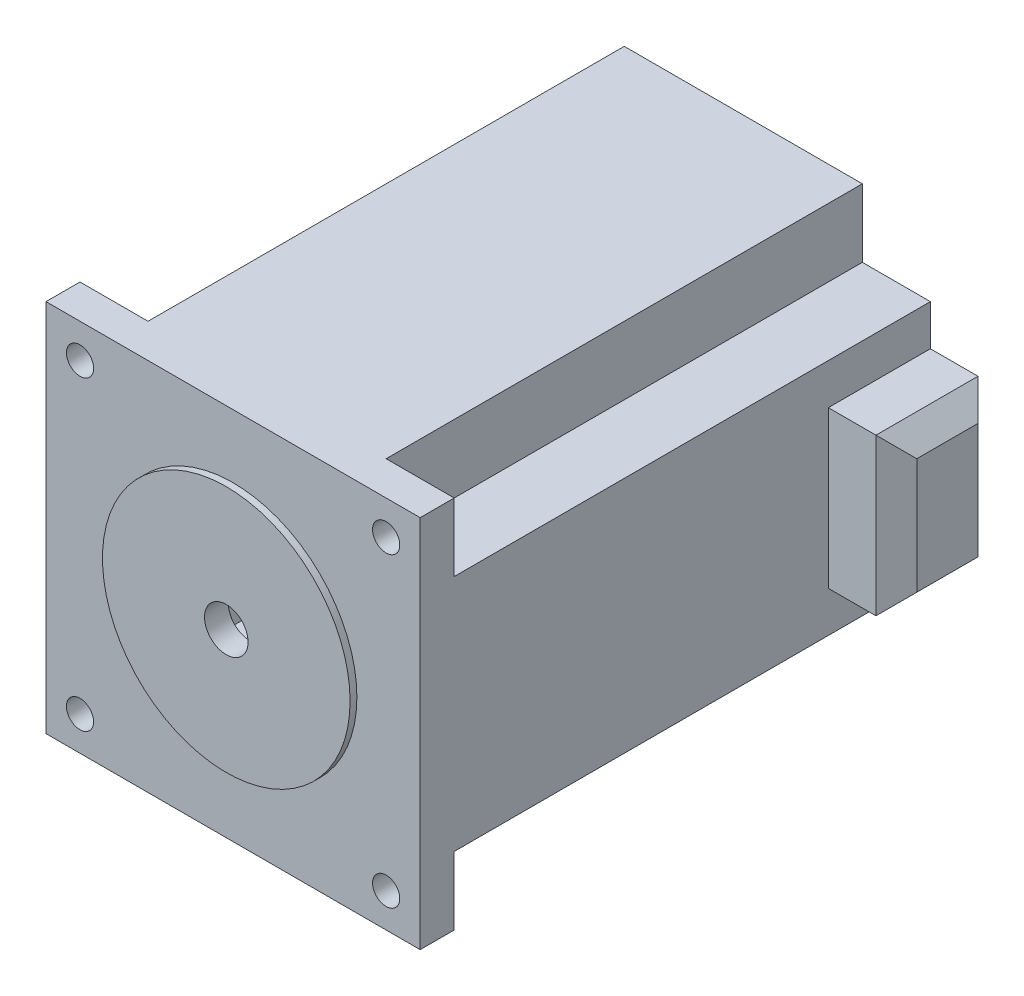
SolidWorks part; units mm, degrees
ref_plane "Front Plane" through (0, 0, 0) normal (0, 0, 1) x (1, 0, 0)
ref_plane "Top Plane" through (0, 0, 0) normal (0, 1, 0) x (1, 0, 0)
ref_plane "Right Plane" through (0, 0, 0) normal (1, 0, 0) x (0, 0, -1)
sketch "Sketch2" plane through (0, 0, 0) normal (0, 0, 1) x (1, 0, 0)
  line L1 (-27.5, 27.5) -> (27.5, 27.5)
  line L2 (-27.5, 27.5) -> (-27.5, -27.5)
  line L3 (-27.5, -27.5) -> (27.5, -27.5)
  line L4 (27.5, 27.5) -> (27.5, -27.5)
  line L5 (-15, 15) -> (15, 15)
  line L6 (-15, 15) -> (-15, -15)
  line L7 (-15, -15) -> (15, -15)
  line L8 (15, 15) -> (15, -15)
  point P9 (0, 15)
  dimension "D1" = 55
  dimension "D2" = 55
  dimension "D3" = 27.5
  dimension "D4" = 27.5
  dimension "D5" = 30
  dimension "D6" = 30
  dimension "D7" = 15
  dimension "D8" = 15
extrude "Boss-Extrude1" add sketch "Sketch2" along normal mid plane 70
sketch "Sketch3" plane through (0, 0, 35) normal (0, 0, 1) x (1, 0, 0)
  line L1 (-27.5, 27.5) -> (27.5, 27.5)
  line L2 (-27.5, 27.5) -> (-27.5, -27.5)
  line L3 (-27.5, -27.5) -> (27.5, -27.5)
  line L4 (27.5, 27.5) -> (27.5, -27.5)
  circle A0 centre (0, 0) radius 3.2
  dimension "D1" = 6.4
extrude "Boss-Extrude2" add sketch "Sketch3" along normal blind 2.5
sketch "Sketch4" plane through (0, 0, -35) normal (0, 0, -1) x (-1, 0, 0)
  line L1 (-27.5, 27.5) -> (27.5, 27.5)
  line L2 (-27.5, 27.5) -> (-27.5, -27.5)
  line L3 (-27.5, -27.5) -> (27.5, -27.5)
  line L4 (27.5, 27.5) -> (27.5, -27.5)
  circle A0 centre (0, 0) radius 3.2
  dimension "D1" = 6.4
extrude "Boss-Extrude3" add sketch "Sketch4" along normal blind 2.5
sketch "Sketch6" plane through (0, 0, 37.5) normal (0, 0, 1) x (1, 0, 0)
  circle A0 centre (0, 0) radius 18.2
  circle A1 centre (0, 0) radius 3.2
  dimension "D1" = 36.4
  dimension "D2" = 6.4
extrude "Boss-Extrude4" add sketch "Sketch6" along normal blind 1
sketch "Sketch7" plane through (27.5, 0, 0) normal (1, 0, 0) x (0, 0, -1)
  line L0 (37.5, 27.5) -> (37.5, -27.5) construction
  line L1 (22.5, 11.5) -> (37.5, 11.5)
  line L2 (22.5, 11.5) -> (22.5, -11.5)
  line L3 (22.5, -11.5) -> (37.5, -11.5)
  line L4 (37.5, 11.5) -> (37.5, -11.5)
  dimension "D1" = 15
  dimension "D2" = 23
  dimension "D3" = 11.5
extrude "Boss-Extrude5" add sketch "Sketch7" along normal blind 10
chamfer "Chamfer1" distance 3 angle 45 4 edges at (37.5, 11.5, -30) (37.5, 0, -37.5) (37.5, -11.5, -30) (37.5, 0, -22.5)
sketch "Sketch8" plane through (0, 0, -37.5) normal (0, 0, -1) x (-1, 0, 0)
  line L1 (-27.5, 27.5) -> (-17.5, 27.5)
  line L2 (-27.5, 27.5) -> (-27.5, 17.5)
  line L3 (-27.5, 17.5) -> (-17.5, 17.5)
  line L4 (-17.5, 27.5) -> (-17.5, 17.5)
  line L5 (27.5, 27.5) -> (17.5, 27.5)
  line L6 (27.5, 27.5) -> (27.5, 17.5)
  line L7 (27.5, 17.5) -> (17.5, 17.5)
  line L8 (17.5, 27.5) -> (17.5, 17.5)
  line L9 (-27.5, -27.5) -> (-17.5, -27.5)
  line L10 (-27.5, -27.5) -> (-27.5, -17.5)
  line L11 (-27.5, -17.5) -> (-17.5, -17.5)
  line L12 (-17.5, -27.5) -> (-17.5, -17.5)
  line L13 (27.5, -27.5) -> (17.5, -27.5)
  line L14 (27.5, -27.5) -> (27.5, -17.5)
  line L15 (27.5, -17.5) -> (17.5, -17.5)
  line L16 (17.5, -27.5) -> (17.5, -17.5)
  dimension "D1" = 10
  dimension "D2" = 10
  dimension "D3" = 10
  dimension "D4" = 10
  dimension "D5" = 10
  dimension "D6" = 10
  dimension "D7" = 10
  dimension "D8" = 10
extrude "Cut-Extrude1" cut sketch "Sketch8" against normal blind 70
sketch "Sketch9" plane through (0, 0, 37.5) normal (0, 0, 1) x (1, 0, 0)
  line L0 (27.5, 27.5) -> (-27.5, 27.5) construction
  line L1 (-27.5, 27.5) -> (-27.5, -27.5) construction
  line L2 (27.5, -27.5) -> (27.5, 27.5) construction
  line L3 (-27.5, -27.5) -> (27.5, -27.5) construction
  circle A0 centre (-22.5, 22.5) radius 2
  circle A1 centre (22.5, 22.5) radius 2
  circle A2 centre (-22.5, -22.5) radius 2
  circle A3 centre (22.5, -22.5) radius 2
  dimension "D1" = 4
  dimension "D2" = 4
  dimension "D3" = 4
  dimension "D4" = 4
  dimension "D5" = 5
  dimension "D6" = 5
  dimension "D7" = 5
  dimension "D8" = 5
  dimension "D9" = 5
  dimension "D10" = 5
  dimension "D11" = 5
  dimension "D12" = 5
extrude "Cut-Extrude2" cut sketch "Sketch9" against normal blind 5
